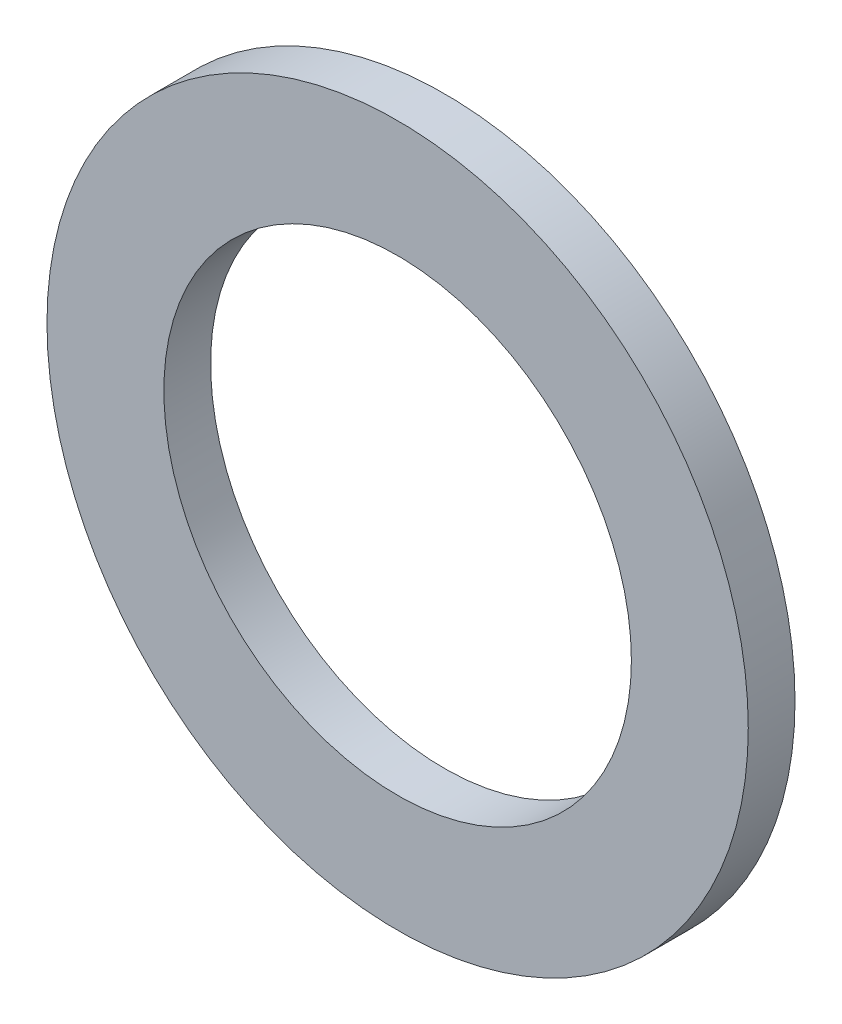
SolidWorks part; units mm, degrees
material "6061-T6 (SS)"
ref_plane "Front Plane" through (0, 0, 0) normal (0, 0, 1) x (1, 0, 0)
ref_plane "Top Plane" through (0, 0, 0) normal (0, 1, 0) x (1, 0, 0)
ref_plane "Right Plane" through (0, 0, 0) normal (1, 0, 0) x (0, 0, -1)
sketch "Sketch1" plane through (0, 0, 0) normal (0, 0, 1) x (1, 0, 0)
  circle A0 centre (0, 0) radius 6.35
  circle A1 centre (0, 0) radius 9.525
  dimension "D1" = 19.05
  dimension "D2" = 12.7
extrude "Boss-Extrude1" add sketch "Sketch1" along normal blind 1.27
